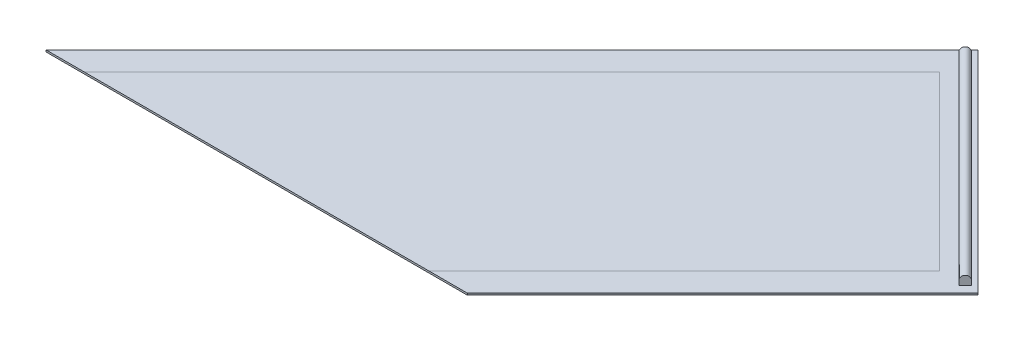
SolidWorks part; units mm, degrees
ref_plane "Front Plane" through (0, 0, 0) normal (0, 0, 1) x (1, 0, 0)
ref_plane "Top Plane" through (0, 0, 0) normal (0, 1, 0) x (1, 0, 0)
ref_plane "Right Plane" through (0, 0, 0) normal (1, 0, 0) x (0, 0, -1)
sketch "Sketch1" plane through (0, 0, 0) normal (0, 1, 0) x (1, 0, 0)
  line L0 (0, -0.4396) -> (0, 0.4515) construction
  line L1 (-0.4325, 0) -> (0.4116, 0) construction
  line L2 (-0.395, 0.395) -> (0.395, -0.395) construction
  line L4 (-49.4975, -516.188) -> (233.3452, -233.3452)
  line L5 (0, 0) -> (233.3452, -233.3452)
  line L6 (-49.4975, -516.188) -> (-282.8427, -282.8427)
  line L7 (0, 0) -> (-282.8427, -282.8427)
  dimension "D1" = 45
  dimension "D2" = 330
  dimension "D3" = 400
extrude "Boss-Extrude1" add sketch "Sketch1" along normal blind 2
sketch "Sketch4" plane through (0, 2, 0) normal (0, 1, 0) x (1, 0, 0)
  line L17 (3.5355, -10.6066) -> (-3.5355, -17.6777)
  line L18 (-3.5355, -17.6777) -> (215.6676, -236.8808)
  line L19 (215.6676, -236.8808) -> (222.7386, -229.8097)
  line L20 (222.7386, -229.8097) -> (3.5355, -10.6066)
  line L21 (0, 0) -> (-282.8427, -282.8427) construction
  line L22 (233.3452, -233.3452) -> (0, 0) construction
  dimension "D1" = 310
  dimension "D2" = 10
  dimension "D3" = 5
  dimension "D4" = 10
extrude "Boss-Extrude2" add sketch "Sketch4" along normal blind 10
sketch "Sketch6" plane through (7.0711, 0, 7.0711) normal (-0.7071, 0, -0.7071) x (-0.7071, 0, 0.7071)
  line L4 (15, 12) -> (15, 2) construction
  line L8 (5, 7) -> (5, 12)
  line L9 (5, 12) -> (15, 12)
  line L10 (5, 12) -> (15, 12) construction
  line L11 (15, 12) -> (15, 7)
  arc A0 (15, 7) -> (5, 7) centre (10, 7) ccw
  line M7 (15, 2) -> (15, 12)
  line M8 (15, 12) -> (5, 12)
  line M9 (5, 12) -> (5, 2)
extrude "Cut-Extrude1" cut sketch "Sketch6" against normal up to next contours A0 L9 M9 | A0 M7 M8
sketch "Sketch10" plane through (0, 0, 0) normal (0, 1, 0) x (1, 0, 0)
  line L0 (-282.8427, -282.8427) -> (-516.188, -516.188)
  line L1 (-516.188, -516.188) -> (-49.4975, -516.188)
  line L2 (0, 0) -> (-282.8427, -282.8427) construction
  line L7 (-282.8427, -282.8427) -> (-49.4975, -516.188)
  line L8 (-49.4975, -516.188) -> (233.3452, -233.3452)
  line L9 (233.3452, -233.3452) -> (0, 0)
  line L10 (0, 0) -> (-282.8427, -282.8427)
  line L11 (-282.8427, -282.8427) -> (-49.4975, -516.188)
  dimension "D1" = 0
extrude "Boss-Extrude3" add sketch "Sketch10" along normal up to surface (2 mm away) up to face at (-24.7487, 2, 258.094)
sketch "Sketch11" plane through (0, 2, 0) normal (0, 1, 0) x (1, 0, 0)
  line L0 (-473.7615, -516.188) -> (-516.188, -516.188)
  line L1 (-70.7107, -494.9747) -> (190.9188, -233.3452) construction
  line L2 (-91.9239, -516.188) -> (190.9188, -233.3452)
  line L3 (190.9188, -233.3452) -> (0, -42.4264)
  line L4 (0, 0) -> (-516.188, -516.188)
  line L5 (-516.188, -516.188) -> (-49.4975, -516.188)
  line L6 (-49.4975, -516.188) -> (233.3452, -233.3452)
  line L7 (233.3452, -233.3452) -> (0, 0)
  line L8 (0, 0) -> (-516.188, -516.188)
  line L10 (-49.4975, -516.188) -> (233.3452, -233.3452)
  line L11 (233.3452, -233.3452) -> (0, 0)
  line L12 (0, -42.4264) -> (-473.7615, -516.188)
  line L13 (0, -42.4264) -> (-494.9747, -537.4012) construction
  line L14 (-516.188, -516.188) -> (-49.4975, -516.188) construction
  line L15 (-91.9239, -516.188) -> (-49.4975, -516.188)
  dimension "D1" = 0
  dimension "D2" = 30
split line "Split Line3"
